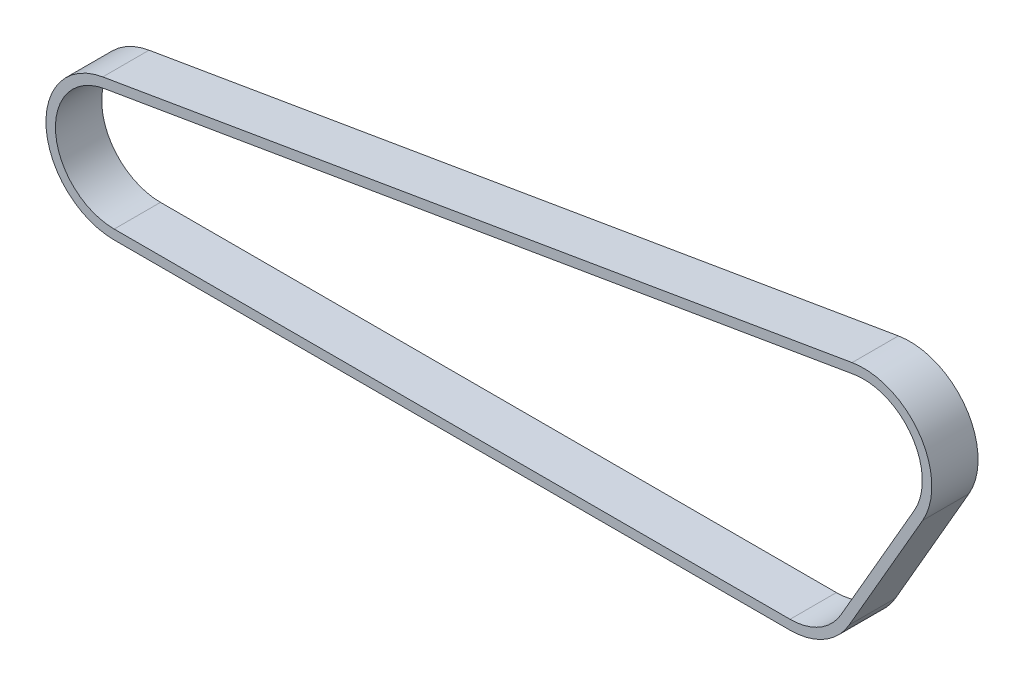
SolidWorks part; units mm, degrees
ref_plane "Front Plane" through (0, 0, 0) normal (0, 0, 1) x (1, 0, 0)
ref_plane "Top Plane" through (0, 0, 0) normal (0, 1, 0) x (1, 0, 0)
ref_plane "Right Plane" through (0, 0, 0) normal (1, 0, 0) x (0, 0, -1)
sketch "Sketch2" plane through (0, 0, 0) normal (0, 0, 1) x (1, 0, 0)
  line L0 (0, 0) -> (1, 0) construction
  line L1 (0, 0) -> (0, 1) construction
  line L2 (21.997, -12.7) -> (-9.753, -67.6926)
  line L3 (-31.75, -80.3926) -> (-323.85, -80.3926)
  line L4 (-328.1023, -29.9511) -> (-4.2523, 25.0415)
  arc A0 (-4.2523, 25.0415) -> (21.997, -12.7) centre (0, 0) cw
  arc A1 (-9.753, -67.6926) -> (-31.75, -80.3926) centre (-31.75, -54.9926) cw
  arc A2 (-323.85, -80.3926) -> (-328.1023, -29.9511) centre (-323.85, -54.9926) cw
sketch "Sketch3" plane through (0, 0, 0) normal (0, 0, 1) x (1, 0, 0)
  line L0 (-328.1023, -29.9511) -> (-4.2523, 25.0415) construction
  line L1 (21.997, -12.7) -> (-9.753, -67.6926) construction
  line L2 (-31.75, -80.3926) -> (-323.85, -80.3926) construction
  line L3 (-328.1023, -29.9511) -> (-4.2523, 25.0415)
  line L4 (21.997, -12.7) -> (-9.753, -67.6926)
  line L5 (-31.75, -80.3926) -> (-323.85, -80.3926)
  line L6 (-328.7887, -25.9089) -> (-4.9387, 29.0837)
  line L7 (25.5477, -14.75) -> (-6.2023, -69.7426)
  line L8 (-31.75, -84.4926) -> (-323.85, -84.4926)
  arc A0 (21.997, -12.7) -> (-4.2523, 25.0415) centre (0, 0) ccw construction
  arc A1 (-31.75, -80.3926) -> (-9.753, -67.6926) centre (-31.75, -54.9926) ccw construction
  arc A2 (-328.1023, -29.9511) -> (-323.85, -80.3926) centre (-323.85, -54.9926) ccw construction
  arc A3 (21.997, -12.7) -> (-4.2523, 25.0415) centre (0, 0) ccw
  arc A4 (-31.75, -80.3926) -> (-9.753, -67.6926) centre (-31.75, -54.9926) ccw
  arc A5 (-328.1023, -29.9511) -> (-323.85, -80.3926) centre (-323.85, -54.9926) ccw
  arc A6 (25.5477, -14.75) -> (-4.9387, 29.0837) centre (0, 0) ccw
  arc A7 (-31.75, -84.4926) -> (-6.2023, -69.7426) centre (-31.75, -54.9926) ccw
  arc A8 (-328.7887, -25.9089) -> (-323.85, -84.4926) centre (-323.85, -54.9926) ccw
  dimension "D1" = 4.1
extrude "Boss-Extrude1" add sketch "Sketch3" along normal mid plane 20
